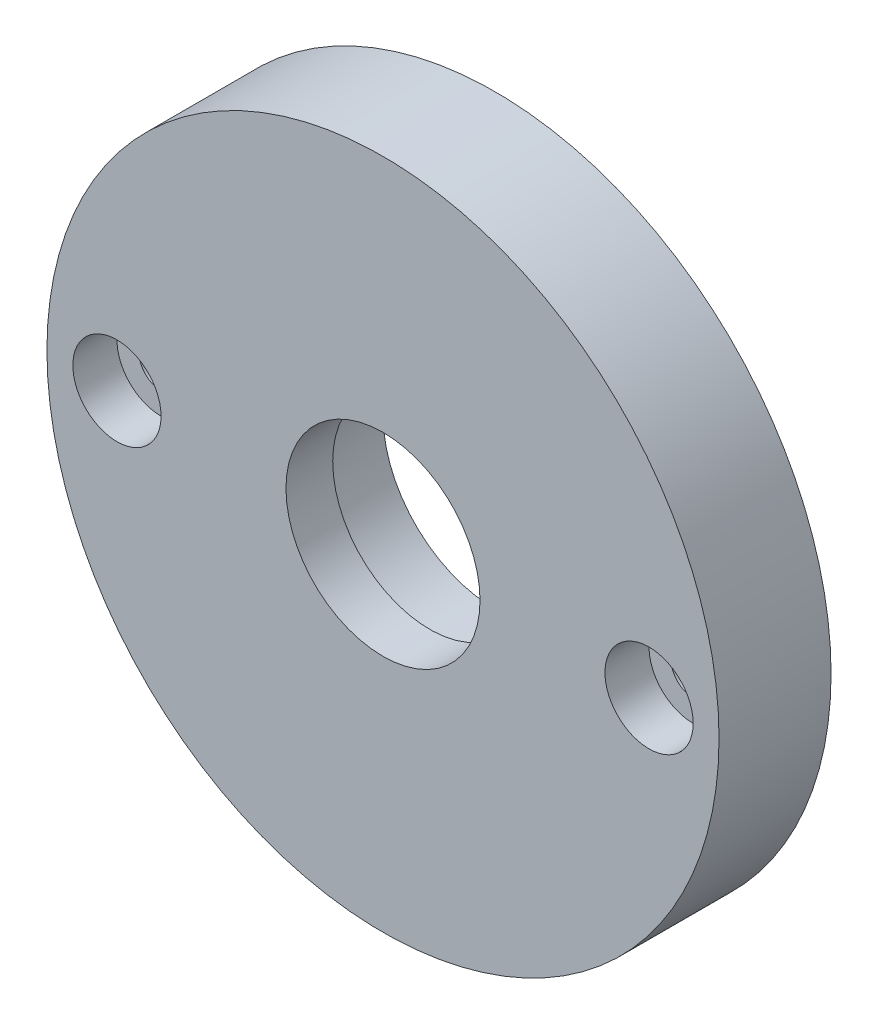
SolidWorks part; units mm, degrees
material "Alliage 1060"
ref_plane "Plan de face" through (0, 0, 0) normal (0, 0, 1) x (1, 0, 0)
ref_plane "Plan de dessus" through (0, 0, 0) normal (0, 1, 0) x (1, 0, 0)
ref_plane "Plan de droite" through (0, 0, 0) normal (1, 0, 0) x (0, 0, -1)
sketch "Esquisse1" plane through (0, 0, 0) normal (0, 0, 1) x (1, 0, 0)
  circle A2 centre (23.0123, 8.4359) radius 38.1
  circle A3 centre (23.0123, 8.4359) radius 11
  dimension "D1" = 76.2
  dimension "D2" = 22
extrude "Boss.-Extru.1" add sketch "Esquisse1" along normal blind 12.7
sketch "Esquisse2" plane through (0, 0, 0) normal (0, 0, -1) x (-1, 0, 0)
  circle A0 centre (-23.0123, 8.4359) radius 12.7
  dimension "D1" = 25.4
extrude "Enlèv. mat.-Extru.1" cut sketch "Esquisse2" against normal blind 7.4
sketch "Esquisse3" plane through (0, 0, 12.7) normal (0, 0, 1) x (1, 0, 0)
  line L0 (-15.0877, 8.4359) -> (61.1123, 8.4359) construction
  circle A0 centre (23.0123, 8.4359) radius 38.1 construction
  circle A1 centre (53.1748, 8.4359) radius 2.5
  circle A2 centre (-7.1502, 8.4359) radius 2.5
  point P7 (23.0123, 8.4359)
  point P12 (23.0123, 8.4359)
  dimension "D1" = 5
  dimension "D2" = 30.1625
  dimension "D3" = 2
extrude "Enlèv. mat.-Extru.2" cut sketch "Esquisse3" against normal through all
sketch "Esquisse4" plane through (0, 0, 12.7) normal (0, 0, 1) x (1, 0, 0)
  circle A0 centre (-7.1502, 8.4359) radius 5
  circle A1 centre (53.1748, 8.4359) radius 5
  dimension "D1" = 10
extrude "Enlèv. mat.-Extru.3" cut sketch "Esquisse4" against normal blind 5
